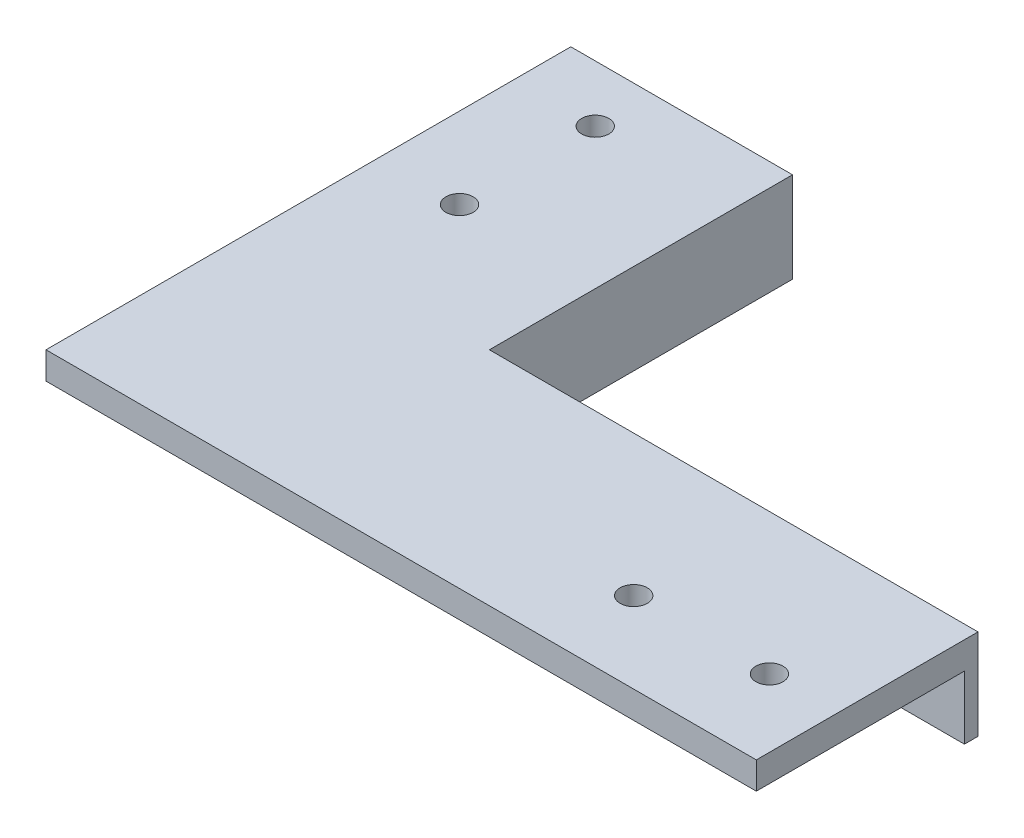
SolidWorks part; units mm, degrees
ref_plane "Alzado" through (0, 0, 0) normal (0, 0, 1) x (1, 0, 0)
ref_plane "Planta" through (0, 0, 0) normal (0, 1, 0) x (1, 0, 0)
ref_plane "Vista lateral" through (0, 0, 0) normal (1, 0, 0) x (0, 0, -1)
sketch "Croquis1" plane through (0, 0, 0) normal (0, 1, 0) x (1, 0, 0)
  line L0 (-16.25, 29) -> (-16.25, -6)
  line L1 (-39.25, -29) -> (39.25, -29) construction
  line L2 (-39.25, -29) -> (-39.25, 29) construction
  line L3 (-39.25, 29) -> (39.25, 29) construction
  line L4 (39.25, -29) -> (39.25, 29) construction
  line L5 (-39.25, -29) -> (39.25, 29) construction
  line L6 (-39.25, 29) -> (39.25, -29) construction
  line L7 (-16.25, -6) -> (39.25, -6)
  line L8 (-16.25, 29) -> (-39.25, 29)
  line L9 (-39.25, 29) -> (-39.25, -29)
  line L10 (-39.25, -29) -> (39.25, -29)
  line L11 (39.25, -29) -> (39.25, -6)
  point P0 (0, 0)
  dimension "D1" = 58
  dimension "D2" = 78.5
  dimension "D3" = 35
  dimension "D4" = 55.5
extrude "Saliente-Extruir1" add sketch "Croquis1" along normal blind 3
sketch "Croquis2" plane through (0, 3, 0) normal (0, 1, 0) x (1, 0, 0)
  line L0 (-39.25, -29) -> (39.25, -29) construction
  line L1 (39.25, -29) -> (39.25, -6) construction
  line L2 (-16.25, 29) -> (-39.25, 29) construction
  line L3 (-39.25, 29) -> (-39.25, -29) construction
  circle A0 centre (31.75, -20.05) radius 1.5
  circle A1 centre (16.75, -20.05) radius 1.5
  circle A2 centre (-30.3, 22.75) radius 1.5
  circle A3 centre (-30.3, 7.75) radius 1.5
  dimension "D4" = 3
  dimension "D6" = 6.25
  dimension "D7" = 8.95
  dimension "D1" = 8.95
  dimension "D2" = 15
  dimension "D3" = 7.5
  dimension "D5" = 15
extrude "Cortar-Extruir2" cut sketch "Croquis2" against normal through all
sketch "Croquis3" plane through (0, 3, 0) normal (0, 1, 0) x (1, 0, 0)
  line L0 (-16.25, 29) -> (-16.25, -6)
  line L1 (-16.25, -6) -> (39.25, -6)
  line L2 (39.25, -6) -> (39.25, -4.5)
  line L3 (39.25, -4.5) -> (-14.75, -4.5)
  line L4 (-14.75, -4.5) -> (-14.75, 29)
  line L5 (-14.75, 29) -> (-16.25, 29)
  dimension "D1" = 1.5
extrude "Saliente-Extruir2" add sketch "Croquis3" against normal blind 10
